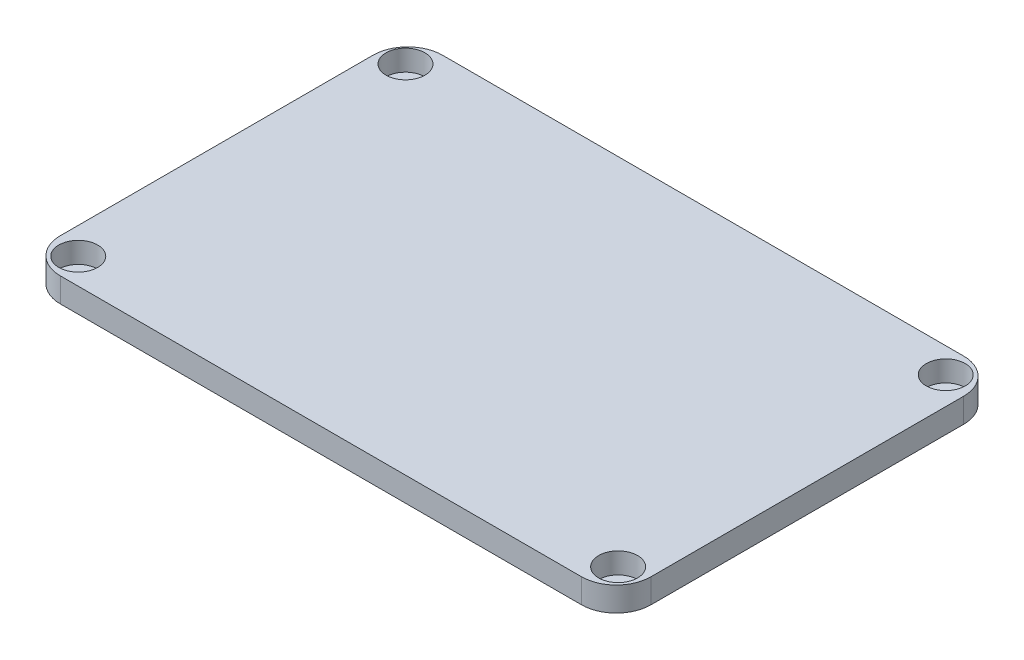
SolidWorks part; units mm, degrees
ref_plane "Front Plane" through (0, 0, 0) normal (0, 0, 1) x (1, 0, 0)
ref_plane "Top Plane" through (0, 0, 0) normal (0, 1, 0) x (1, 0, 0)
ref_plane "Right Plane" through (0, 0, 0) normal (1, 0, 0) x (0, 0, -1)
sketch "Sketch1" plane through (0, 0, 0) normal (0, 1, 0) x (1, 0, 0)
  line L1 (-20.6225, 7.5653) -> (54.3775, 7.5653)
  line L2 (-25.6225, 2.5653) -> (-25.6225, -42.4347)
  line L3 (-20.6225, -47.4347) -> (54.3775, -47.4347)
  line L4 (59.3775, 2.5653) -> (59.3775, -42.4347)
  arc A0 (54.3775, -47.4347) -> (59.3775, -42.4347) centre (54.3775, -42.4347) ccw
  arc A1 (-20.6225, -47.4347) -> (-25.6225, -42.4347) centre (-20.6225, -42.4347) cw
  arc A2 (59.3775, 2.5653) -> (54.3775, 7.5653) centre (54.3775, 2.5653) ccw
  arc A3 (-25.6225, 2.5653) -> (-20.6225, 7.5653) centre (-20.6225, 2.5653) cw
  point P7 (59.3775, -47.4347)
  point P12 (59.3775, 7.5653)
  point P15 (-25.6225, 7.5653)
  dimension "D3" = 5
  dimension "D1" = 85
  dimension "D2" = 55
extrude "Boss-Extrude1" add sketch "Sketch1" along normal blind 3.5
sketch "Sketch2" plane through (0, 3.5, 0) normal (0, 1, 0) x (1, 0, 0)
  circle A0 centre (-22.1876, 3.8027) radius 2.8
  circle A3 centre (-21.7754, -43.6973) radius 2.8
  circle A4 centre (55.4124, 3.9479) radius 2.8
  circle A5 centre (55.7665, -43.5521) radius 2.8
  point P8 (0, 0)
  point P9 (0, 0)
  point P10 (0, 0)
  point P11 (0, 0)
  point P12 (0, 0)
  dimension "D1" = 47.5
  dimension "D2" = 47.5
  dimension "D3" = 77.6
extrude "Cut-Extrude1" cut sketch "Sketch2" against normal blind 3
